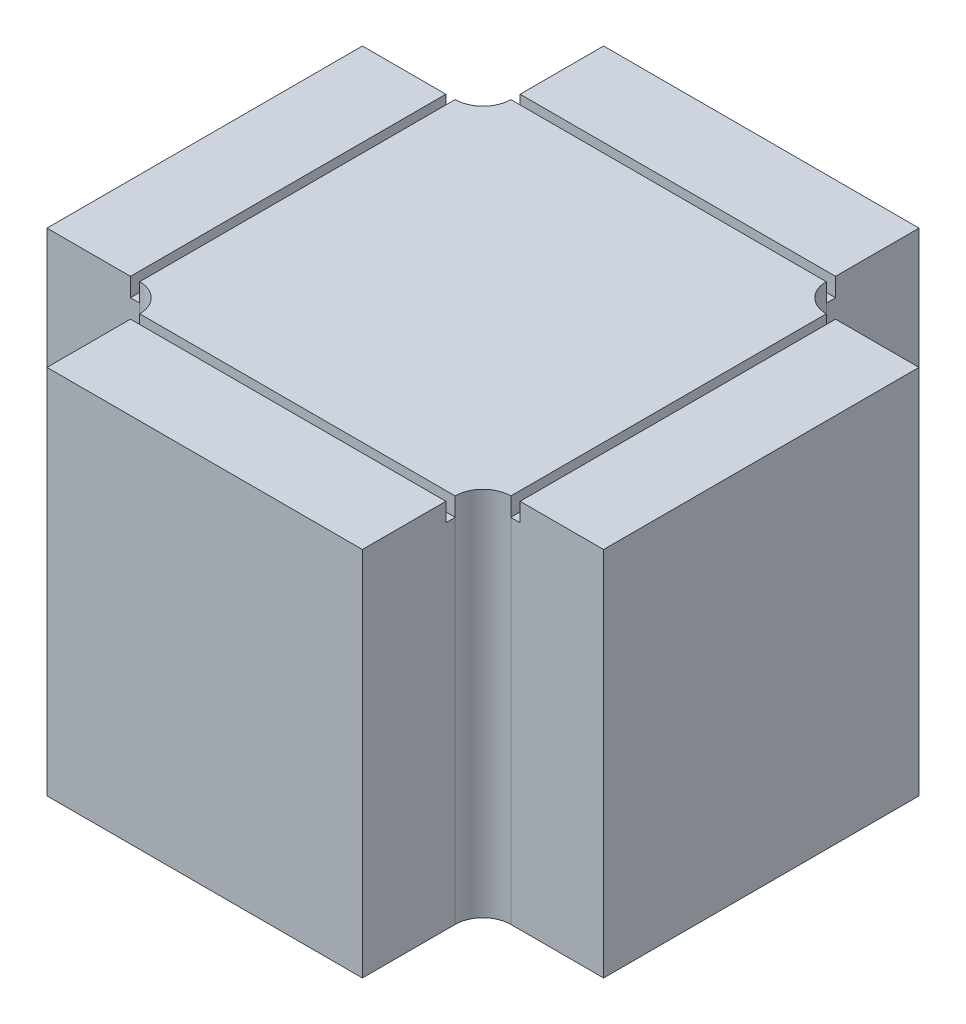
SolidWorks part; units mm, degrees
ref_plane "Front Plane" through (0, 0, 0) normal (0, 0, 1) x (1, 0, 0)
ref_plane "Top Plane" through (0, 0, 0) normal (0, 1, 0) x (1, 0, 0)
ref_plane "Right Plane" through (0, 0, 0) normal (1, 0, 0) x (0, 0, -1)
sketch "Sketch1" plane through (0, 0, 0) normal (0, 1, 0) x (1, 0, 0)
  line L5 (-20, -20) -> (20, 20) construction
  line L6 (-20, 20) -> (20, -20) construction
  line L7 (-20, 17) -> (-30, 17)
  line L9 (-20, -17) -> (-30, -17)
  line L10 (-30, 17) -> (-30, -17)
  line L11 (17, 20) -> (17, 30)
  line L12 (17, 30) -> (-17, 30)
  line L13 (-17, 20) -> (-17, 30)
  line L14 (20, -17) -> (30, -17)
  line L15 (30, -17) -> (30, 17)
  line L16 (20, 17) -> (30, 17)
  line L17 (-17, -20) -> (-17, -30)
  line L18 (-17, -30) -> (17, -30)
  line L19 (17, -20) -> (17, -30)
  circle A0 centre (-20, -20) radius 3
  circle A1 centre (-20, 20) radius 3
  circle A2 centre (20, 20) radius 3
  circle A3 centre (20, -20) radius 3
  point P0 (0, 0)
  point P7 (0, 0)
  point P16 (0, 0)
  point P33 (0, 0)
  dimension "D3" = 6
  dimension "D1" = 40
  dimension "D2" = 40
  dimension "D5" = 34
  dimension "D6" = 10
  dimension "D4" = 4
  dimension "D7" = 4
extrude "Boss-Extrude1" add sketch "Sketch1" along normal blind 40
sketch "Sketch3" plane through (0, 40, 0) normal (0, 1, 0) x (1, 0, 0)
  line L0 (-21, -21) -> (-21, 21)
  line L1 (-20, -20) -> (20, -20)
  line L2 (-20, -20) -> (-20, 20)
  line L3 (-20, 20) -> (20, 20)
  line L4 (20, -20) -> (20, 20)
  line L5 (-20, -20) -> (20, 20) construction
  line L6 (-20, 20) -> (20, -20) construction
  line L7 (-21, 21) -> (21, 21)
  line L8 (21, -21) -> (21, 21)
  line L9 (-21, -21) -> (21, -21)
  point P0 (0, 0)
  dimension "D1" = 1
sketch "Sketch4" plane through (0, 0, 30) normal (0, 0, 1) x (1, 0, 0)
  circle A0 centre (-20, 40) radius 1
extrude "Cut-Extrude2" cut sketch "Sketch3" against normal blind 2 contours L2 L3 L4 L1 | L0 L7 L8 L9
